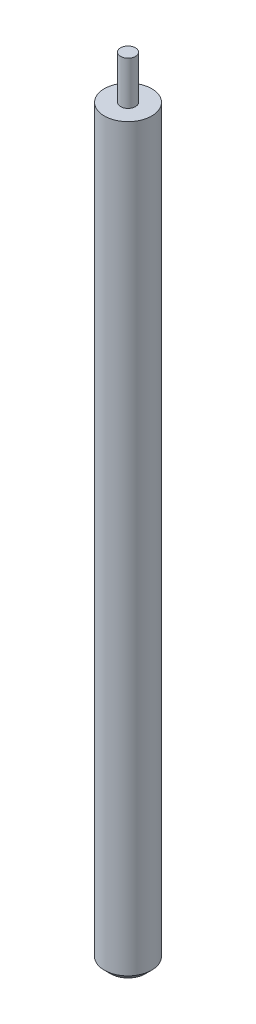
SolidWorks part; units mm, degrees
material "AISI 1020"
ref_plane "Plano frontal" through (0, 0, 0) normal (0, 0, 1) x (1, 0, 0)
ref_plane "Plano superior" through (0, 0, 0) normal (0, 1, 0) x (1, 0, 0)
ref_plane "Plano direito" through (0, 0, 0) normal (1, 0, 0) x (0, 0, -1)
sketch "Esboço1" plane through (0, 0, 0) normal (0, 0, 1) x (1, 0, 0)
  line L0 (0, 0) -> (0, 1284.819) construction
  line L1 (0, 635) -> (6, 635)
  line L2 (6, 635) -> (6, 600)
  line L3 (6, 600) -> (19.05, 600)
  line L4 (19.05, 600) -> (19.05, 0)
  line L5 (19.05, 0) -> (0, 0)
  line L6 (0, 0) -> (0, 635)
  dimension "D1" = 12
  dimension "D2" = 38.1
  dimension "D3" = 35
  dimension "D4" = 600
revolve "Revolução1" add sketch "Esboço1" angle 360 about L0
chamfer "Chanfro1" distance 5 angle 45 1 edges at (0, 0, -19.05)
